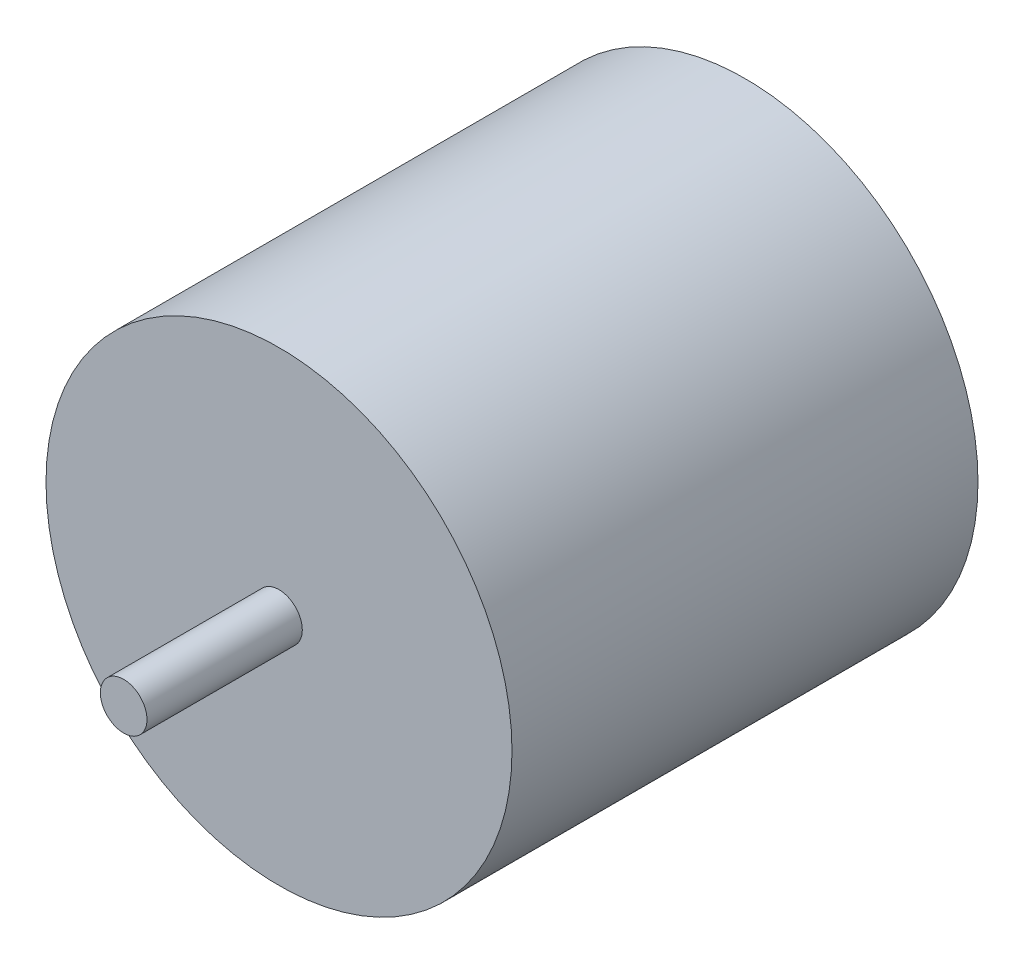
SolidWorks part; units mm, degrees
ref_plane "Front Plane" through (0, 0, 0) normal (0, 0, 1) x (1, 0, 0)
ref_plane "Top Plane" through (0, 0, 0) normal (0, 1, 0) x (1, 0, 0)
ref_plane "Right Plane" through (0, 0, 0) normal (1, 0, 0) x (0, 0, -1)
sketch "Sketch1" plane through (0, 0, 0) normal (0, 0, 1) x (1, 0, 0)
  circle A0 centre (0, 0) radius 15
  dimension "D1" = 30
extrude "Boss-Extrude1" add sketch "Sketch1" along normal blind 30
sketch "Sketch2" plane through (0, 0, 30) normal (0, 0, 1) x (1, 0, 0)
  circle A0 centre (0, 0) radius 1.5
  dimension "D1" = 3
extrude "Boss-Extrude2" add sketch "Sketch2" along normal blind 10
sketch "Sketch3" plane through (0, 0, 0) normal (0, 0, -1) x (-1, 0, 0)
  line L0 (0, 17.0579) -> (0, -20.8248) construction
  line L1 (-7, -1.6234) -> (-5, -1.6234)
  line L2 (-7, -1.6234) -> (-7, 2.3766)
  line L3 (-7, 2.3766) -> (-5, 2.3766)
  line L4 (-5, -1.6234) -> (-5, 2.3766)
  line L5 (-7, -1.6234) -> (-5, 2.3766) construction
  line L6 (-7, 2.3766) -> (-5, -1.6234) construction
  line L7 (7, 2.3766) -> (5, -1.6234) construction
  line L8 (7, -1.6234) -> (5, 2.3766) construction
  line L9 (5, -1.6234) -> (5, 2.3766)
  line L10 (7, 2.3766) -> (5, 2.3766)
  line L11 (7, -1.6234) -> (7, 2.3766)
  line L12 (7, -1.6234) -> (5, -1.6234)
  point P0 (-6, 0.3766)
  point P12 (6, 0.3766)
  dimension "D1" = 2
  dimension "D2" = 4
  dimension "D3" = 6
extrude "Boss-Extrude3" add sketch "Sketch3" along normal blind 5
